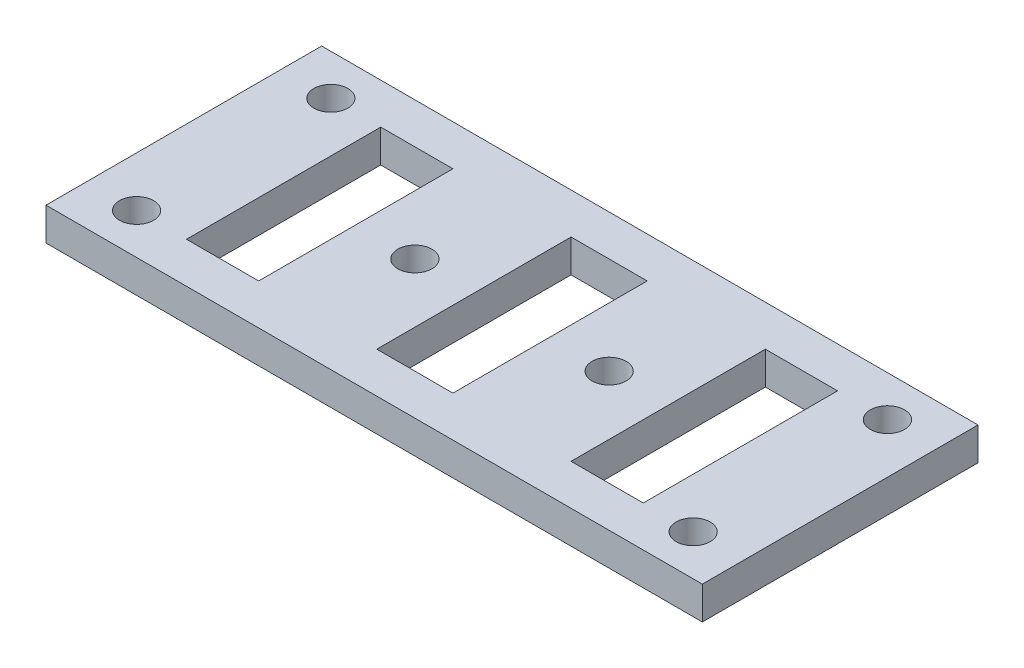
SolidWorks part; units mm, degrees
ref_plane "Front Plane" through (0, 0, 0) normal (0, 0, 1) x (1, 0, 0)
ref_plane "Top Plane" through (0, 0, 0) normal (0, 1, 0) x (1, 0, 0)
ref_plane "Right Plane" through (0, 0, 0) normal (1, 0, 0) x (0, 0, -1)
sketch "Sketch1" plane through (0, 0, 0) normal (0, 1, 0) x (1, 0, 0)
  line L1 (-55.2275, 35.9417) -> (71.7725, 35.9417)
  line L2 (-55.2275, 35.9417) -> (-55.2275, -17.3983)
  line L3 (-55.2275, -17.3983) -> (71.7725, -17.3983)
  line L4 (71.7725, 35.9417) -> (71.7725, -17.3983)
  line L5 (-35.9235, -9.5243) -> (-21.9535, -9.5243)
  line L6 (-35.9235, -9.5243) -> (-35.9235, 28.0677)
  line L7 (-35.9235, 28.0677) -> (-21.9535, 28.0677)
  line L8 (-21.9535, -9.5243) -> (-21.9535, 28.0677)
  line L9 (52.4685, -9.5243) -> (38.4985, -9.5243)
  line L10 (52.4685, -9.5243) -> (52.4685, 28.0677)
  line L11 (52.4685, 28.0677) -> (38.4985, 28.0677)
  line L12 (38.4985, -9.5243) -> (38.4985, 28.0677)
  line L13 (0.9065, -9.5243) -> (15.6385, -9.5243)
  line L14 (0.9065, -9.5243) -> (0.9065, 28.0677)
  line L15 (0.9065, 28.0677) -> (15.6385, 28.0677)
  line L16 (15.6385, -9.5243) -> (15.6385, 28.0677)
  circle A0 centre (-45.5755, -9.5243) radius 3.302
  circle A1 centre (-45.5755, 28.0677) radius 3.302
  circle A2 centre (62.1205, -9.5243) radius 3.302
  circle A3 centre (62.1205, 28.0677) radius 3.302
  circle A4 centre (-10.5235, 9.2717) radius 3.302
  circle A5 centre (27.0685, 9.2717) radius 3.302
  dimension "D9" = 9.652
  dimension "D11" = 6.604
  dimension "D12" = 6.604
  dimension "D13" = 6.604
  dimension "D14" = 6.604
  dimension "D17" = 6.604
  dimension "D18" = 6.604
  dimension "D1" = 127
  dimension "D2" = 53.34
  dimension "D3" = 37.592
  dimension "D4" = 37.592
  dimension "D5" = 7.874
  dimension "D6" = 7.874
  dimension "D7" = 7.874
  dimension "D8" = 7.874
  dimension "D10" = 9.652
  dimension "D15" = 9.652
  dimension "D16" = 37.592
  dimension "D19" = 26.67
  dimension "D20" = 26.67
  dimension "D21" = 11.43
  dimension "D22" = 11.43
  dimension "D23" = 11.43
  dimension "D24" = 44.704
  dimension "D25" = 19.304
  dimension "D26" = 11.43
  dimension "D27" = 19.304
  dimension "D28" = 9.652
extrude "Boss-Extrude1" add sketch "Sketch1" along normal blind 6.35
